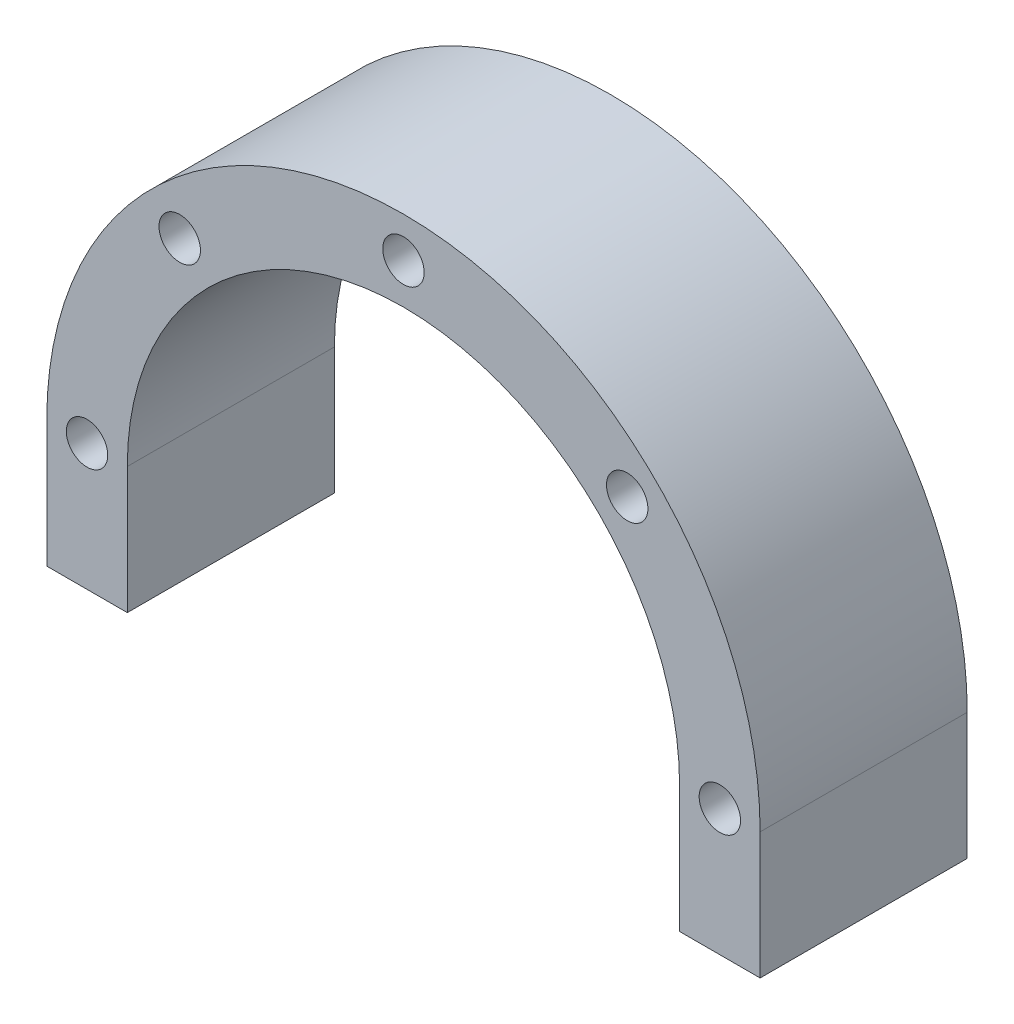
SolidWorks part; units mm, degrees
material "ABS"
ref_plane "正面" through (0, 0, 0) normal (0, 0, 1) x (1, 0, 0)
ref_plane "平面" through (0, 0, 0) normal (0, 1, 0) x (1, 0, 0)
ref_plane "右側面" through (0, 0, 0) normal (1, 0, 0) x (0, 0, -1)
sketch "ｽｹｯﾁ1" plane through (0, 0, 0) normal (0, 0, 1) x (1, 0, 0)
  line L0 (0, -1000) -> (0, 49000) construction
  line L1 (-31, -11) -> (31, -11)
  line L2 (-31, 0) -> (-31, -11)
  line L4 (31, -11) -> (31, 0)
  circle A0 centre (0, 0) radius 31 construction
  arc A2 (-31, 0) -> (31, 0) centre (0, 0) cw
  point P3 (0, -31)
  dimension "D1" = 62
  dimension "D2" = 20
extrude "ﾎﾞｽ - 押し出し1" add sketch "ｽｹｯﾁ1" along normal blind 18 contours A2 L2 L1 L4
sketch "ｽｹｯﾁ2" plane through (0, 0, 18) normal (0, 0, 1) x (1, 0, 0)
  line L4 (-31, -11) -> (31, -11) construction
  line L9 (-24, 0) -> (-24, -11)
  line L11 (24, -11) -> (24, 0)
  line L12 (24, -11) -> (-24, -11)
  arc A1 (31, 0) -> (-31, 0) centre (0, 0) ccw construction
  arc A3 (24, 0) -> (-24, 0) centre (0, 0) ccw
  dimension "D1" = 24
extrude "ｶｯﾄ - 押し出し1" cut sketch "ｽｹｯﾁ2" against normal through all
hole_wizard "M3 すきま穴1" positions "ｽｹｯﾁ3" profile "ｽｹｯﾁ4" hole size "M3" standard "JIS" end condition through all
sketch "ｽｹｯﾁ3" plane through (0, 0, 18) normal (0, 0, 1) x (1, 0, 0)
  point P0 (0, 27.5)
  dimension "D1" = 27.5
sketch "ｽｹｯﾁ4" plane through (0, 27.5, 18) normal (1, 0, 0) x (0, -1, 0)
  line L0 (0, 0) -> (0, 18)
  line L1 (0, 18) -> (1.8, 18)
  line L2 (1.8, 18) -> (1.8, 0)
  line L5 (1.8, 0) -> (0, 0)
  line L11 (0, -6.35) -> (0, 107.95) construction
  dimension "通し穴の直径" = 3.6
  dimension "通し穴の深さ" = 18
pattern_circular "円形ﾊﾟﾀｰﾝ1" count 8 over 360 about axis through (0, 0, 0) along (0, 0, 1) skipping 3, 4, 5 of "M3 すきま穴1"
